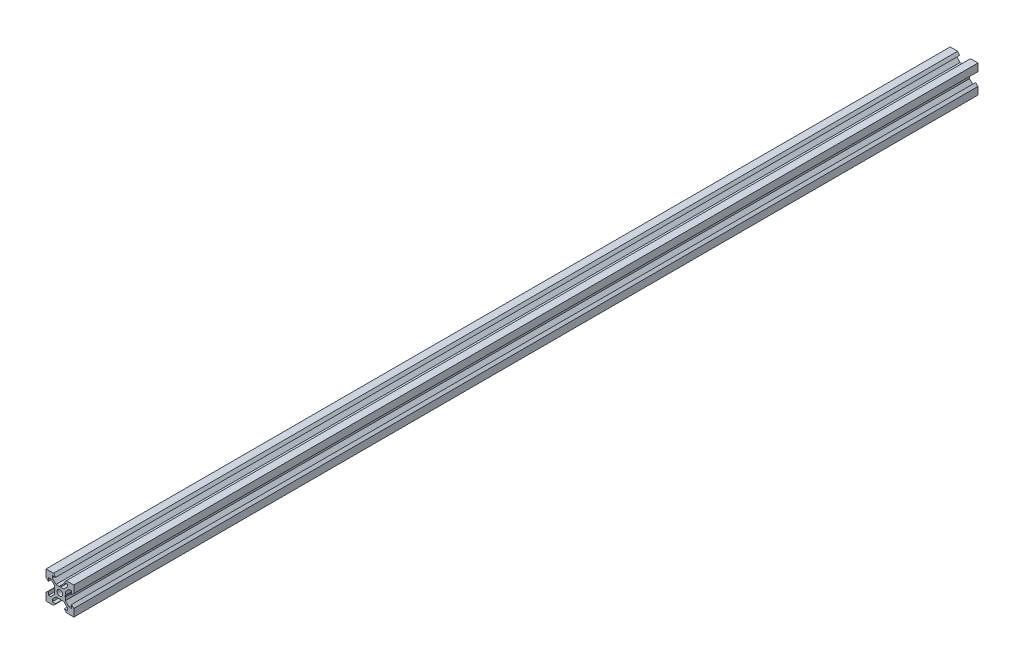
SolidWorks part; units mm, degrees
ref_plane "Front Plane" through (0, 0, 0) normal (0, 0, 1) x (1, 0, 0)
ref_plane "Top Plane" through (0, 0, 0) normal (0, 1, 0) x (1, 0, 0)
ref_plane "Right Plane" through (0, 0, 0) normal (1, 0, 0) x (0, 0, -1)
sketch "Sketch1" plane through (0, 0, 0) normal (0, 0, 1) x (1, 0, 0)
  line L0 (10, 10) -> (4.6104, 10) construction
  line L1 (10, 10) -> (10, 4.6104) construction
  line L2 (10, -10) -> (10, -4.6104) construction
  line L3 (10, -10) -> (4.6104, -10) construction
  line L4 (10, 10) -> (10, 4.6104)
  line L5 (6.5607, 5.5) -> (8.2, 5.5)
  line L6 (5.5, 8.2) -> (5.5, 6.5607)
  line L7 (10, 10) -> (4.6104, 10)
  line L8 (10, 10) -> (10, 4.6104)
  line L9 (6.5607, 5.5) -> (3.9, 2.8393)
  line L10 (5.5, 6.5607) -> (2.8393, 3.9)
  line L11 (10, 4.6104) -> (8.2, 3.1)
  line L12 (4.6104, 10) -> (3.1, 8.2)
  line L13 (8.2, 3.1) -> (8.2, 5.5)
  line L14 (3.1, 8.2) -> (5.5, 8.2)
  line L15 (-6.5607, 5.5) -> (-8.2, 5.5)
  line L16 (6.5607, -5.5) -> (8.2, -5.5)
  line L17 (3.1, -8.2) -> (5.5, -8.2)
  line L18 (8.2, -3.1) -> (8.2, -5.5)
  line L19 (4.6104, -10) -> (3.1, -8.2)
  line L20 (10, -4.6104) -> (8.2, -3.1)
  line L21 (0.5196, -3.9) -> (0, -3.6)
  line L22 (0.5196, 3.9) -> (0, 3.6)
  line L23 (3.6, 0) -> (3.9, -0.5196)
  line L24 (3.9, 0.5196) -> (3.6, 0)
  line L25 (3.9, 0.5196) -> (3.9, 2.8393)
  line L26 (2.8393, 3.9) -> (0.5196, 3.9)
  line L27 (3.9, -2.8393) -> (3.9, -0.5196)
  line L28 (2.8393, -3.9) -> (0.5196, -3.9)
  line L29 (5.5, -6.5607) -> (2.8393, -3.9)
  line L30 (6.5607, -5.5) -> (3.9, -2.8393)
  line L31 (10, -10) -> (10, -4.6104)
  line L32 (10, -10) -> (4.6104, -10)
  line L33 (5.5, -8.2) -> (5.5, -6.5607)
  line L34 (-6.5607, -5.5) -> (-8.2, -5.5)
  line L35 (10, -10) -> (10, -4.6104)
  line L36 (0, 0) -> (0, 8.2) construction
  line L37 (-10, -10) -> (-4.6104, -10) construction
  line L38 (-10, -10) -> (-10, -4.6104) construction
  line L39 (-10, 10) -> (-10, 4.6104) construction
  line L40 (-10, 10) -> (-4.6104, 10) construction
  line L41 (-10, -10) -> (-10, -4.6104)
  line L43 (-5.5, -8.2) -> (-5.5, -6.5607)
  line L44 (-10, -10) -> (-4.6104, -10)
  line L45 (-10, -10) -> (-10, -4.6104)
  line L46 (-6.5607, -5.5) -> (-3.9, -2.8393)
  line L47 (-5.5, -6.5607) -> (-2.8393, -3.9)
  line L48 (-2.8393, -3.9) -> (-0.5196, -3.9)
  line L49 (-3.9, -2.8393) -> (-3.9, -0.5196)
  line L50 (-2.8393, 3.9) -> (-0.5196, 3.9)
  line L51 (-3.9, 0.5196) -> (-3.9, 2.8393)
  line L52 (-3.9, 0.5196) -> (-3.6, 0)
  line L53 (-3.6, 0) -> (-3.9, -0.5196)
  line L54 (-0.5196, 3.9) -> (0, 3.6)
  line L55 (-0.5196, -3.9) -> (0, -3.6)
  line L56 (-10, -4.6104) -> (-8.2, -3.1)
  line L57 (-4.6104, -10) -> (-3.1, -8.2)
  line L58 (-8.2, -3.1) -> (-8.2, -5.5)
  line L59 (-3.1, -8.2) -> (-5.5, -8.2)
  line L60 (-10, -10) -> (10, -10) construction
  line L61 (-10, -10) -> (-10, 10) construction
  line L62 (-3.1, 8.2) -> (-5.5, 8.2)
  line L63 (-8.2, 3.1) -> (-8.2, 5.5)
  line L64 (-4.6104, 10) -> (-3.1, 8.2)
  line L65 (-10, 4.6104) -> (-8.2, 3.1)
  line L66 (-5.5, 6.5607) -> (-2.8393, 3.9)
  line L67 (-6.5607, 5.5) -> (-3.9, 2.8393)
  line L68 (-10, 10) -> (-10, 4.6104)
  line L69 (-10, 10) -> (-4.6104, 10)
  line L70 (-5.5, 8.2) -> (-5.5, 6.5607)
  line L71 (-10, 10) -> (10, 10) construction
  line L72 (-10, 10) -> (-10, 4.6104)
  line L73 (10, -10) -> (10, 10) construction
  line L74 (-10, -10) -> (10, 10) construction
  line L75 (-10, 10) -> (10, -10) construction
  circle A0 centre (0, 0) radius 2
  dimension "D7" = 4
  dimension "D1" = 20
  dimension "D2" = 5.3896
  dimension "D3" = 4.5
  dimension "D4" = 50
  dimension "D5" = 1.8
  dimension "D6" = 1.5104
  dimension "D8" = 5.5
  dimension "D9" = 120
  dimension "D10" = 0.3
  dimension "D11" = 2.3197
  dimension "D12" = 7.8
  dimension "D13" = 7.8
  dimension "D14" = 1.5
  dimension "D15" = 2.6607
extrude "Boss-Extrude1" add sketch "Sketch1" along normal mid plane 650 contours L70 L62 L64 L69 L68 L65 L63 L15 L67 L51 L52 L53 L49 L46 L34 L58 L56 L41 L44 L57 L59 L43 L47 L48 L55 L21 L28 L29 L33 L17 L19 L32 L31 L20 L18 L16 L30 L27 L23 L24 L25 L9 L5 L13 L11 L4 L7 L12 L14 L6 L10
